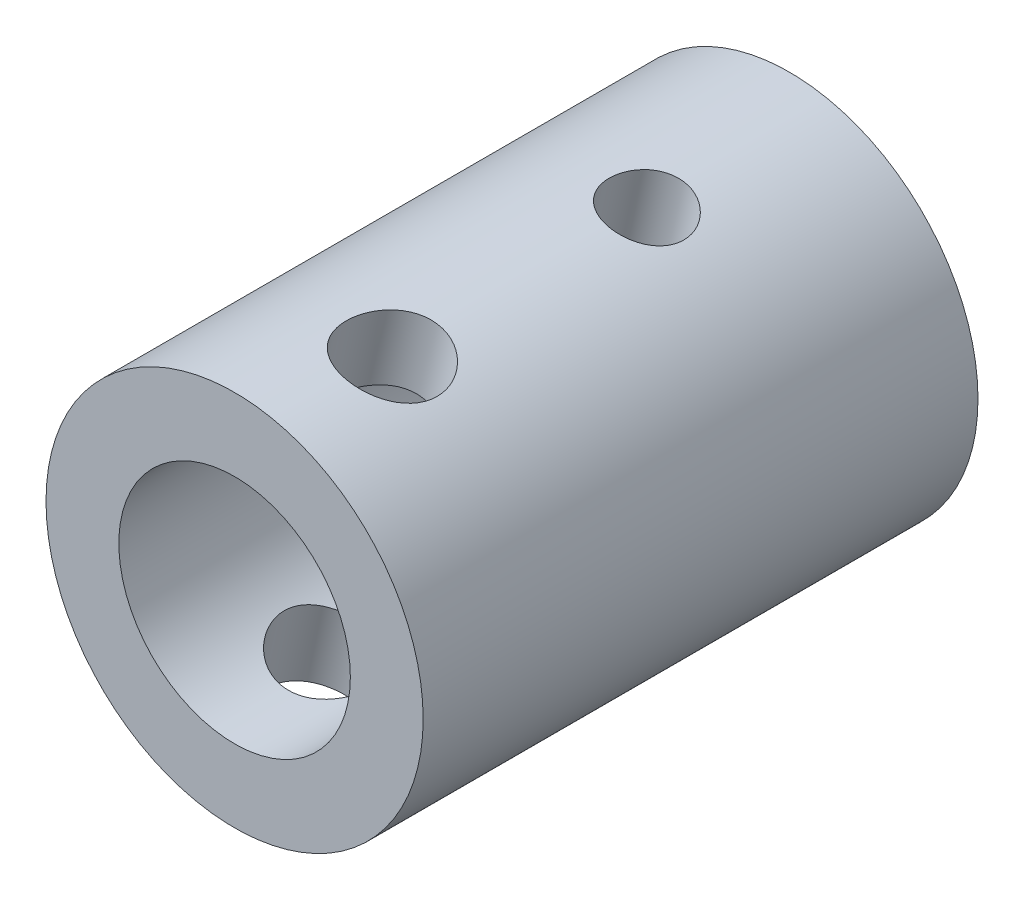
SolidWorks part; units mm, degrees
ref_plane "Front Plane" through (0, 0, 0) normal (0, 0, 1) x (1, 0, 0)
ref_plane "Top Plane" through (0, 0, 0) normal (0, 1, 0) x (1, 0, 0)
ref_plane "Right Plane" through (0, 0, 0) normal (1, 0, 0) x (0, 0, -1)
sketch "Sketch1" plane through (0, 0, 0) normal (0, 0, 1) x (1, 0, 0)
  circle A0 centre (0, 0) radius 25.9
extrude "Boss-Extrude1" add sketch "Sketch1" along normal blind 76.2
sketch "Sketch2" plane through (0, 0, 76.2) normal (0, 0, 1) x (1, 0, 0)
  circle A0 centre (0, 0) radius 15.9
extrude "Cut-Extrude1" cut sketch "Sketch2" against normal blind 75
hole_wizard "Ø10.5 (10.5) Diameter Hole1" positions "3DSketch1" profile "Sketch3" hole size "Ø10.5" standard "Ansi Metric"
sketch3d "3DSketch1"
  line L0 (0, 0, 0) -> (5.4829, 25.313, 0)
  line L3 (5.4829, 25.313, 0) -> (5.4829, 25.313, 25)
  circle A0 centre (0, 0, 0) radius 25.9 construction
  point P0 (5.4829, 25.313, 25)
  point P7 (0, 0, 25.9)
  dimension "D1" = 25
sketch "Sketch3" plane through (5.4829, 25.313, 25) normal (0, 0, 1) x (-0.9773, 0.2117, 0)
  line L0 (0, 0) -> (0, 23.1545)
  line L1 (0, 23.1545) -> (5.25, 20)
  line L2 (5.25, 20) -> (5.25, 0)
  line L5 (5.25, 0) -> (0, 0)
  line L10 (0, 23.1545) -> (-5.25, 20) construction
  line L11 (0, -6.35) -> (0, 107.95) construction
  dimension "Hole Dia." = 10.5
  dimension "Hole Depth" = 20
  dimension "Drill Angle" = 118
hole_wizard "Ø12.8 (12.8) Diameter Hole1" positions "3DSketch2" profile "Sketch4" hole size "Ø12.8" standard "Ansi Metric"
sketch3d "3DSketch2"
  line L0 (5.5559, 25.2971, 19.7505) -> (5.5559, 25.2971, 0)
  line L3 (5.5559, 25.2971, 0) -> (5.5559, 25.2971, 60)
  circle A0 centre (0, 0, 0) radius 25.9 construction
  spline S0 degree 3 poles (0.2381, 25.8989, 25.3478) (0.2381, 25.8989, 24.6522) (0.2731, 25.8987, 24.3104) (0.3755, 25.8973, 23.8062) (0.4181, 25.8967, 23.6396) (0.5203, 25.8948, 23.3094) (0.5802, 25.8936, 23.1455) (0.7815, 25.8886, 22.669) (0.9455, 25.8835, 22.3678) (1.3316, 25.8665, 21.7978) (1.5552, 25.8544, 21.5287) (2.042, 25.8205, 21.0458) (2.3071, 25.7987, 20.8288) (2.8814, 25.7408, 20.445) (3.1849, 25.7054, 20.2825) (3.6555, 25.6412, 20.0858) (3.8154, 25.618, 20.0279) (4.1411, 25.5673, 19.9277) (4.308, 25.5398, 19.8852) (4.8093, 25.4518, 19.7838) (5.1443, 25.3863, 19.7502) (5.8155, 25.241, 19.7498) (6.155, 25.1603, 19.7841) (6.8081, 24.9915, 19.9184) (7.1242, 24.903, 20.0178) (7.5831, 24.7655, 20.2157) (7.7339, 24.7188, 20.2901) (8.024, 24.6262, 20.4524) (8.1642, 24.58, 20.5405) (8.5701, 24.4427, 20.8251) (8.8229, 24.3522, 21.0431) (9.2848, 24.1798, 21.5309) (9.4891, 24.0999, 21.795) (9.8469, 23.9559, 22.3626) (10.0015, 23.8914, 22.67) (10.2483, 23.7866, 23.3044) (10.3415, 23.7459, 23.6316) (10.4678, 23.6905, 24.3063) (10.5, 23.6762, 24.6548) (10.5002, 23.676, 25.3409) (10.4693, 23.6898, 25.6826) (10.3431, 23.7452, 26.3629) (10.2491, 23.7862, 26.6927) (10.0651, 23.8644, 27.1668) (9.9965, 23.8932, 27.3218) (9.8443, 23.9563, 27.6253) (9.7603, 23.9907, 27.7744) (9.4907, 24.0993, 28.203) (9.2865, 24.1791, 28.4668) (8.8288, 24.35, 28.9512) (8.5731, 24.4417, 29.1726) (8.0314, 24.6249, 29.5529) (7.7435, 24.7174, 29.7146) (7.2844, 24.855, 29.9134) (7.1267, 24.9008, 29.9723) (6.8091, 24.9895, 30.0725) (6.6484, 25.0327, 30.1143) (6.1604, 25.159, 30.2151) (5.8253, 25.2388, 30.2498) (5.1477, 25.3857, 30.2502) (4.8125, 25.4512, 30.2165) (4.1491, 25.5677, 30.083) (3.8177, 25.6191, 29.9816) (3.1873, 25.7051, 29.7188) (2.8864, 25.7403, 29.5578) (2.4571, 25.7836, 29.2717) (2.3171, 25.7965, 29.1683) (2.05, 25.8191, 28.9503) (1.9225, 25.8288, 28.8355) (1.5574, 25.8543, 28.4738) (1.3371, 25.8662, 28.2096) (0.9468, 25.8834, 27.6348) (0.7827, 25.8885, 27.3331) (0.5153, 25.8952, 26.7018) (0.4114, 25.8968, 26.3686) (0.2731, 25.8987, 25.6911) (0.2381, 25.8989, 25.3478) (0.2381, 25.8989, 24.6522) (0.2731, 25.8987, 24.3104) knots -0.03125 -0.03125 0 0 0.03125 0.03125 0.046875 0.046875 0.0625 0.0625 0.09375 0.09375 0.125 0.125 0.15625 0.15625 0.1875 0.1875 0.203125 0.203125 0.21875 0.21875 0.25 0.25 0.28125 0.28125 0.3125 0.3125 0.328125 0.328125 0.34375 0.34375 0.375 0.375 0.40625 0.40625 0.4375 0.4375 0.46875 0.46875 0.5 0.5 0.53125 0.53125 0.5625 0.5625 0.578125 0.578125 0.59375 0.59375 0.625 0.625 0.65625 0.65625 0.6875 0.6875 0.703125 0.703125 0.71875 0.71875 0.75 0.75 0.78125 0.78125 0.8125 0.8125 0.84375 0.84375 0.859375 0.859375 0.875 0.875 0.90625 0.90625 0.9375 0.9375 0.96875 0.96875 1 1 1.03125 1.03125 1.046875 only from (0.2381, 25.8989, 25) to (0.2381, 25.8989, 25) construction
  point P0 (5.5559, 25.2971, 60)
  point P6 (0, 0, 25.9)
  dimension "D1" = 60
sketch "Sketch4" plane through (5.5559, 25.2971, 60) normal (0, 0, 1) x (-0.9767, 0.2145, 0)
  line L0 (0, 0) -> (0, 303.8455)
  line L1 (0, 303.8455) -> (6.4, 300)
  line L2 (6.4, 300) -> (6.4, 0)
  line L5 (6.4, 0) -> (0, 0)
  line L10 (0, 303.8455) -> (-6.4, 300) construction
  line L11 (0, -6.35) -> (0, 107.95) construction
  dimension "Hole Dia." = 12.8
  dimension "Hole Depth" = 300
  dimension "Drill Angle" = 118
